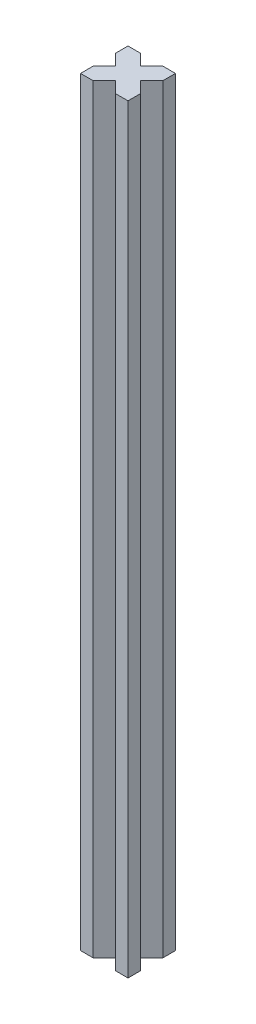
SolidWorks part; units mm, degrees
ref_plane "Front" through (0, 0, 0) normal (0, 0, 1) x (1, 0, 0)
ref_plane "Top" through (0, 0, 0) normal (0, 1, 0) x (1, 0, 0)
ref_plane "Right" through (0, 0, 0) normal (1, 0, 0) x (0, 0, -1)
sketch "Sketch1" plane through (0, 0, 0) normal (0, 1, 0) x (1, 0, 0)
  line L0 (0, 0) -> (4, 0)
  line L1 (0, 0) -> (0, 4)
  line L2 (15, 0) -> (15, 4)
  line L3 (0, 15) -> (4, 15)
  line L4 (4, 15) -> (7.5, 11.5)
  line L5 (7.5, 11.5) -> (11, 15)
  line L6 (15, 11) -> (11.5, 7.5)
  line L7 (11.5, 7.5) -> (15, 4)
  line L8 (11, 0) -> (7.5, 3.5)
  line L9 (7.5, 3.5) -> (4, 0)
  line L10 (0, 4) -> (3.5, 7.5)
  line L11 (3.5, 7.5) -> (0, 11)
  line L12 (-50, 0) -> (50, 0) construction
  line L13 (0, -50) -> (0, 50) construction
  line L14 (11, 15) -> (15, 15)
  line L15 (15, 11) -> (15, 15)
  line L16 (0, 11) -> (0, 15)
  line L17 (11, 0) -> (15, 0)
  dimension "D1" = 15
  dimension "D2" = 15
  dimension "D3" = 7
  dimension "D4" = 135
  dimension "D5" = 135
  dimension "D6" = 45
  dimension "D7" = 45
  dimension "D8" = 7
  dimension "D9" = 7
  dimension "D10" = 7
extrude "Boss-Extrude1" add sketch "Sketch1" along normal blind 240
